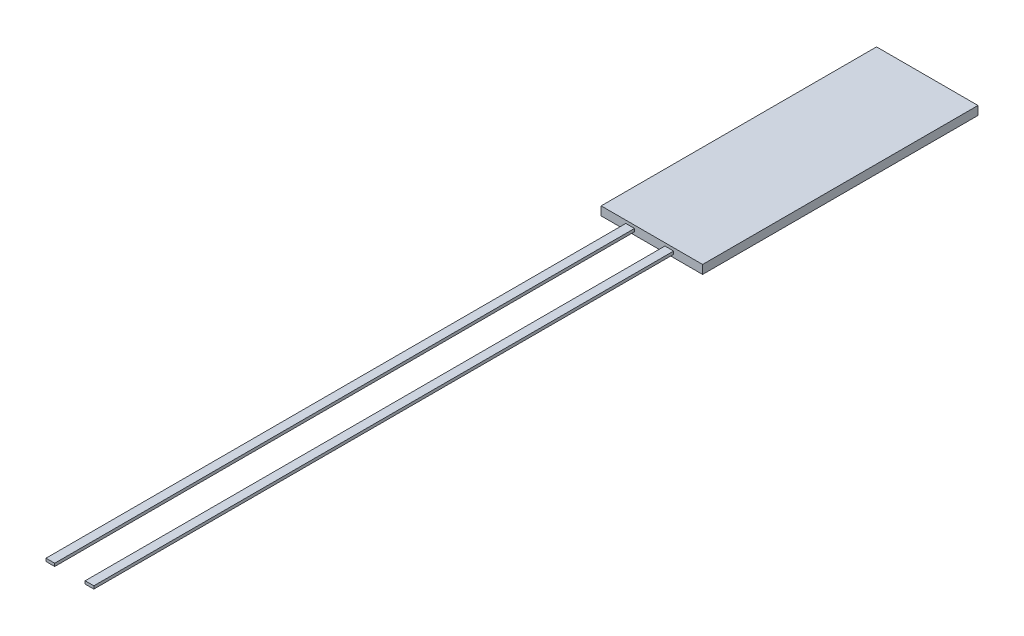
SolidWorks part; units mm, degrees
material "Pure Gold"
ref_plane "Front Plane" through (0, 0, 0) normal (0, 0, 1) x (1, 0, 0)
ref_plane "Top Plane" through (0, 0, 0) normal (0, 1, 0) x (1, 0, 0)
ref_plane "Right Plane" through (0, 0, 0) normal (1, 0, 0) x (0, 0, -1)
sketch "Sketch2" plane through (0, 0, 0) normal (0, 1, 0) x (1, 0, 0)
  line L1 (-1.75, 4.75) -> (1.75, 4.75)
  line L2 (-1.75, 4.75) -> (-1.75, -4.75)
  line L3 (-1.75, -4.75) -> (1.75, -4.75)
  line L4 (1.75, 4.75) -> (1.75, -4.75)
  line L5 (-1.75, 4.75) -> (1.75, -4.75) construction
  line L6 (-1.75, -4.75) -> (1.75, 4.75) construction
  point P0 (0, 0)
  dimension "D1" = 9.5
  dimension "D2" = 3.5
extrude "Boss-Extrude1" add sketch "Sketch2" along normal blind 0.3
sketch "Sketch3" plane through (0, 0, 4.75) normal (0, 0, 1) x (1, 0, 0)
  line L0 (-1.75, 0.15) -> (1.75, 0.15) construction
  line L1 (-1.75, 0.3) -> (-1.75, 0) construction
  line L2 (1.75, 0.3) -> (1.75, 0) construction
  line L3 (-1.75, 0.15) -> (-0.75, 0.15) construction
  line L5 (-0.9, 0.2) -> (-0.6, 0.2)
  line L6 (-0.9, 0.2) -> (-0.9, 0.1)
  line L7 (-0.9, 0.1) -> (-0.6, 0.1)
  line L8 (-0.6, 0.2) -> (-0.6, 0.1)
  line L9 (-0.9, 0.2) -> (-0.6, 0.1) construction
  line L10 (-0.9, 0.1) -> (-0.6, 0.2) construction
  line L13 (0, 0) -> (0, 0.15) construction
  line L14 (-1.75, 0) -> (1.75, 0) construction
  line L15 (0.45, 0.2) -> (0.45, 0.1)
  line L16 (0.45, 0.2) -> (0.75, 0.2)
  line L17 (0.75, 0.2) -> (0.75, 0.1)
  line L18 (0.45, 0.1) -> (0.75, 0.1)
  point P16 (0.75, 0.15)
  dimension "D1" = 0.1
  dimension "D2" = 0.3
  dimension "D3" = 1
  dimension "D4" = 2
  dimension "D5" = 1
extrude "Boss-Extrude2" add sketch "Sketch3" along normal blind 20
